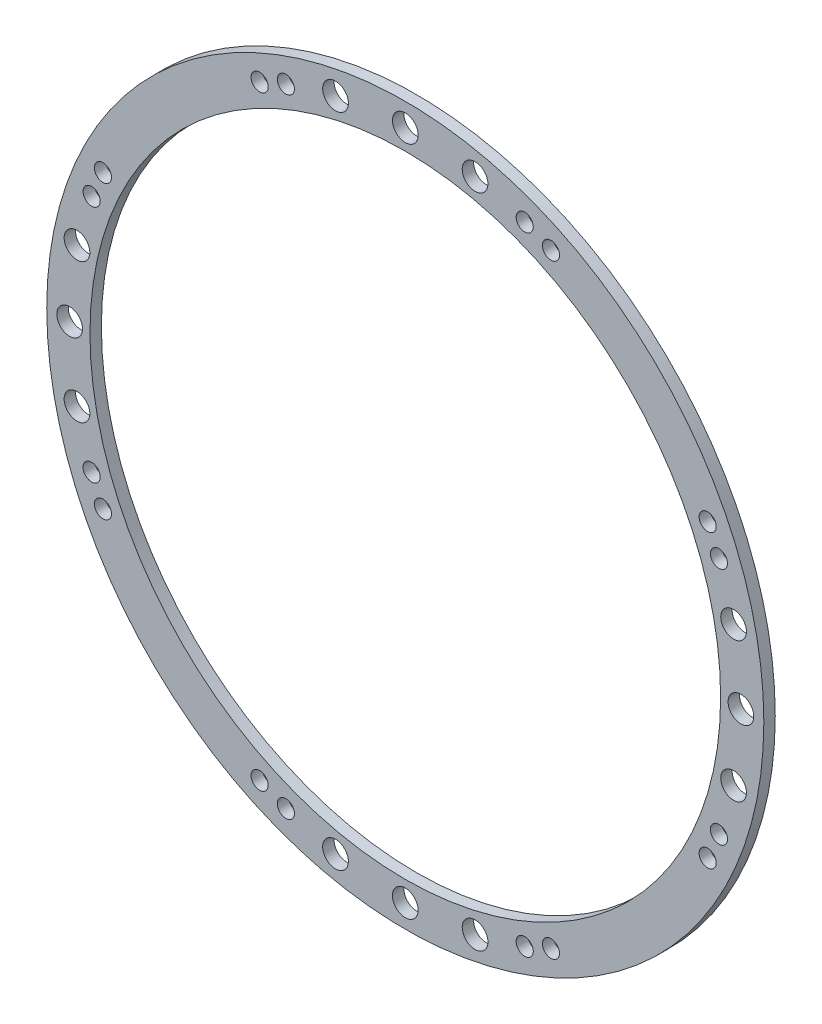
SolidWorks part; units mm, degrees
ref_plane "Front Plane" through (0, 0, 0) normal (0, 0, 1) x (1, 0, 0)
ref_plane "Top Plane" through (0, 0, 0) normal (0, 1, 0) x (1, 0, 0)
ref_plane "Right Plane" through (0, 0, 0) normal (1, 0, 0) x (0, 0, -1)
sketch "Sketch1" plane through (0, 0, 0) normal (0, 0, 1) x (1, 0, 0)
  line L0 (-48.8585, 10.3852) -> (0, 0) construction
  line L1 (0, 0) -> (-10.3852, 48.8585) construction
  line L2 (-48.8585, 10.3852) -> (-43.3808, 9.2209) construction
  line L3 (-10.3852, 48.8585) -> (-9.2209, 43.3808) construction
  line L4 (-31.3602, 31.3602) -> (0, 0) construction
  line L5 (0, 0) -> (-36.1773, 0) construction
  arc A0 (-9.2209, 43.3808) -> (-43.3808, 9.2209) centre (0, 0) ccw construction
  arc A1 (-10.3852, 48.8585) -> (-48.8585, 10.3852) centre (0, 0) ccw construction
  circle A2 centre (0, 0) radius 49.95 construction
  circle A3 centre (0, 0) radius 44.35 construction
  circle A4 centre (0, 0) radius 49.95 construction
  circle A5 centre (0, 0) radius 44.35 construction
  circle A6 centre (-9.7698, 45.9632) radius 1.8 construction
  circle A7 centre (-9.7698, 45.9632) radius 1.8 construction
  circle A10 centre (0, 0) radius 50.2 construction
  circle A11 centre (0, 0) radius 50.2
  circle A12 centre (0, 0) radius 44.15 construction
  circle A13 centre (0, 0) radius 44.15
extrude "Boss-Extrude1" add sketch "Sketch1" along normal blind 1.6
sketch "Sketch2" plane through (0, 0, 1.6) normal (0, 0, 1) x (1, 0, 0)
  circle A0 centre (-45.9632, 9.7698) radius 1.8 construction
  circle A1 centre (-9.7698, 45.9632) radius 1.8 construction
  circle A2 centre (-45.9632, 9.7698) radius 1.8
  circle A3 centre (-9.7698, 45.9632) radius 1.8
  circle A4 centre (-16.7196, 43.9149) radius 1 construction
  circle A5 centre (-20.3938, 42.3338) radius 1 construction
  circle A6 centre (-42.3338, 20.3938) radius 1 construction
  circle A7 centre (-43.9149, 16.7196) radius 1 construction
  circle A8 centre (-16.7196, 43.9149) radius 1 construction
  circle A9 centre (-20.3938, 42.3338) radius 1 construction
  circle A10 centre (-42.3338, 20.3938) radius 1 construction
  circle A11 centre (-43.9149, 16.7196) radius 1 construction
  circle A12 centre (-42.3338, 20.3938) radius 1.2
  circle A13 centre (-43.9149, 16.7196) radius 1.2
  circle A14 centre (-20.3938, 42.3338) radius 1.2
  circle A15 centre (-16.7196, 43.9149) radius 1.2
  circle A16 centre (-46.99, 0) radius 1.8 construction
  circle A17 centre (0, 46.99) radius 1.8 construction
  circle A18 centre (-46.99, 0) radius 1.8
  circle A19 centre (0, 46.99) radius 1.8
  dimension "D1" = 0.2
extrude "Cut-Extrude1" cut sketch "Sketch2" against normal through all
pattern_circular "CirPattern1" count 4 over 360 about axis through (0, 0, 0) along (0, 0, 1) of "Cut-Extrude1"
